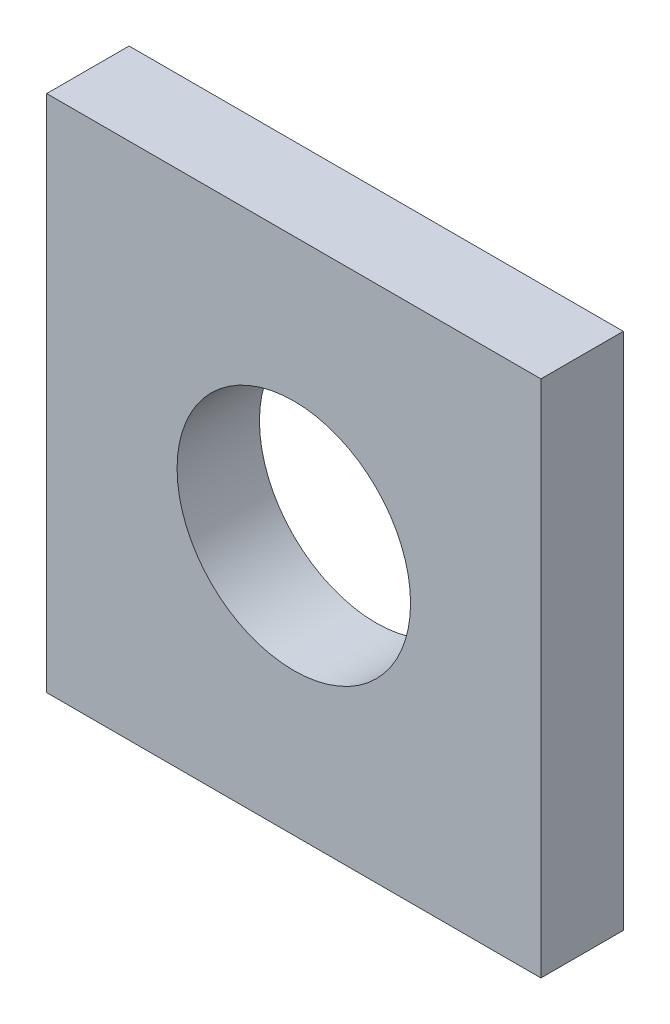
SolidWorks part; units mm, degrees
material "Copper"
ref_plane "Front Plane" through (0, 0, 0) normal (0, 0, 1) x (1, 0, 0)
ref_plane "Top Plane" through (0, 0, 0) normal (0, 1, 0) x (1, 0, 0)
ref_plane "Right Plane" through (0, 0, 0) normal (1, 0, 0) x (0, 0, -1)
sketch "Sketch1" plane through (0, 0, 0) normal (0, 0, 1) x (1, 0, 0)
  line L1 (-7.475, 10) -> (-26.525, 10)
  line L2 (-7.475, 10) -> (-7.475, -10)
  line L3 (-7.475, -10) -> (-26.525, -10)
  line L4 (-26.525, 10) -> (-26.525, -10)
  line L5 (-26.525, 10) -> (-7.475, -10) construction
  line L7 (-26.525, -10) -> (-7.475, 10) construction
  line L9 (-13.825, -10) -> (-13.825, -22.675) construction
  line L10 (-13.825, -22.675) -> (-20.175, -22.675) construction
  line L11 (-20.175, -10) -> (-20.175, -22.675) construction
  line L12 (-7.475, -10) -> (-13.825, -10) construction
  line L13 (-20.175, -10) -> (-26.525, -10) construction
  line L14 (-8.1971, -10) -> (-25.8029, -10) construction
  point P5 (0, 0)
  point P6 (-6.8835, -10.7512)
  point P13 (-17, 10)
  point P15 (-17, -19.5)
  point P17 (-17, -22.675)
  point P18 (-17, 0)
  dimension "D1" = 6.35
  dimension "D2" = 19.5
  dimension "D3" = 3.175
  dimension "D4" = 19.05
extrude "Boss-Extrude1" add sketch "Sketch1" along normal blind 3.175 contours L4 L3 L2 L1
hole_wizard "BMS #4-40 Tapped Hole" [suppressed] positions "Sketch3" profile "Sketch4" tap size "#4-40" standard "ANSI Inch"
sketch "Sketch3" plane through (0, 0, 4.7625) normal (0, 0, 1) x (1, 0, 0)
  point P0 (-17, -19.5)
sketch "Sketch4" plane through (-17, -19.5, 4.7625) normal (1, 0, 0) x (0, -1, 0)
  line L0 (0, 0) -> (0, 4.7625)
  line L1 (0, 4.7625) -> (1.1303, 4.7625)
  line L2 (1.1303, 4.7625) -> (1.1303, 0)
  line L5 (1.1303, 0) -> (0, 0)
  line L11 (0, -6.35) -> (0, 107.95) construction
  dimension "Thru Tap Drill Dia." = 2.2606
  dimension "Thru Tap Drill Depth" = 4.7625
cosmetic thread "Hole Thread1" [suppressed] parameters "D2"=2.8448
hole_wizard "Cell Module Terminal M8 Clearance Hole\\" positions "Sketch5" profile "Sketch6" hole size "M8" standard "ANSI Metric" end condition through all
sketch "Sketch5" plane through (0, 0, 3.175) normal (0, 0, 1) x (1, 0, 0)
  point P0 (-17, 0)
sketch "Sketch6" plane through (-17, 0, 3.175) normal (1, 0, 0) x (0, -1, 0)
  line L0 (0, 0) -> (0, 3.175)
  line L1 (0, 3.175) -> (4.5, 3.175)
  line L2 (4.5, 3.175) -> (4.5, 0)
  line L5 (4.5, 0) -> (0, 0)
  line L11 (0, -6.35) -> (0, 107.95) construction
  dimension "Thru Hole Dia." = 9
  dimension "Thru Hole Depth" = 3.175
